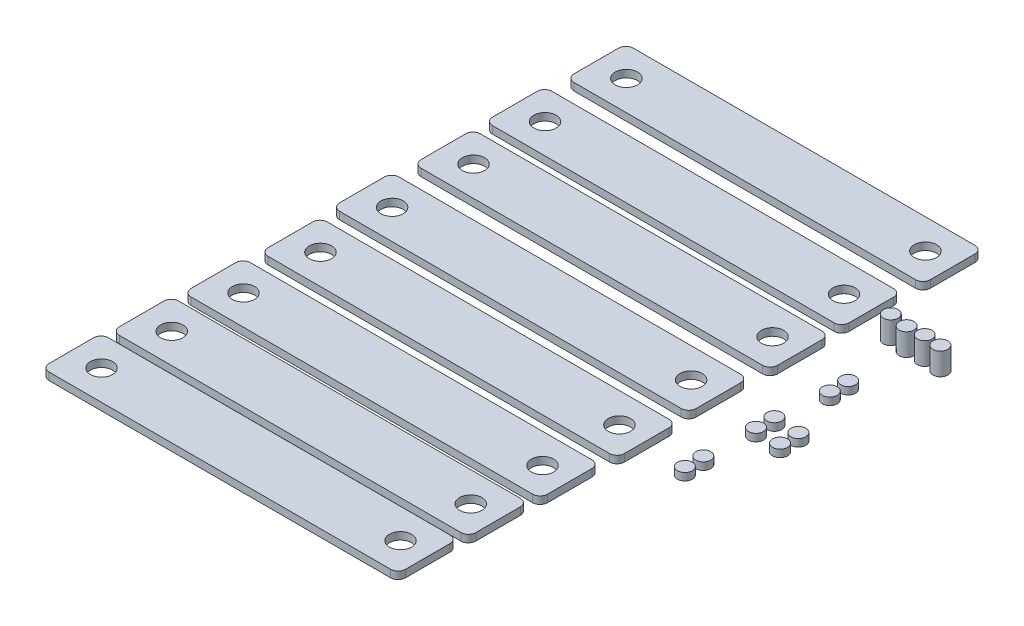
SolidWorks part; units mm, degrees
ref_plane "Front Plane" through (0, 0, 0) normal (0, 0, 1) x (1, 0, 0)
ref_plane "Top Plane" through (0, 0, 0) normal (0, 1, 0) x (1, 0, 0)
ref_plane "Right Plane" through (0, 0, 0) normal (1, 0, 0) x (0, 0, -1)
sketch "Sketch3" plane through (0, 0, 0) normal (0, 1, 0) x (1, 0, 0)
  line L0 (-120.2705, -22.8298) -> (109.7295, -22.8298)
  line L1 (-118.0489, 29.7498) -> (111.9511, 29.7498)
  line L2 (-123.0489, 24.7498) -> (-123.0489, -5.2502)
  line L3 (-118.0489, -10.2502) -> (111.9511, -10.2502)
  line L4 (116.9511, 24.7498) -> (116.9511, -5.2502)
  line L5 (-125.2705, -27.8298) -> (-125.2705, -57.8298)
  line L6 (-120.2705, -62.8298) -> (109.7295, -62.8298)
  line L7 (114.7295, -27.8298) -> (114.7295, -57.8298)
  line L8 (-120.3658, -122.7974) -> (109.6342, -122.7974)
  line L9 (-125.3658, -127.7974) -> (-125.3658, -157.7974)
  line L10 (-120.3658, -162.7974) -> (109.6342, -162.7974)
  line L11 (114.6342, -127.7974) -> (114.6342, -157.7974)
  line L12 (-118.1707, -73.1877) -> (111.8293, -73.1877)
  line L13 (-123.1707, -78.1877) -> (-123.1707, -108.1877)
  line L14 (-118.1707, -113.1877) -> (111.8293, -113.1877)
  line L15 (116.8293, -78.1877) -> (116.8293, -108.1877)
  line L16 (-122.1219, -169.334) -> (107.8781, -169.334)
  line L17 (-127.1219, -174.334) -> (-127.1219, -204.334)
  line L18 (-122.1219, -209.334) -> (107.8781, -209.334)
  line L19 (112.8781, -174.334) -> (112.8781, -204.334)
  line L20 (-118.7564, 78.6191) -> (111.2436, 78.6191)
  line L21 (-116.5347, 131.1987) -> (113.4653, 131.1987)
  line L22 (-121.5347, 126.1987) -> (-121.5347, 96.1987)
  line L23 (-116.5347, 91.1987) -> (113.4653, 91.1987)
  line L24 (118.4653, 126.1987) -> (118.4653, 96.1987)
  line L25 (-123.7564, 73.6191) -> (-123.7564, 43.6191)
  line L26 (-118.7564, 38.6191) -> (111.2436, 38.6191)
  line L27 (116.2436, 73.6191) -> (116.2436, 43.6191)
  line L28 (-124.3751, -214.3962) -> (105.6249, -214.3962)
  line L29 (-129.3751, -219.3962) -> (-129.3751, -249.3962)
  line L30 (-124.3751, -254.3962) -> (105.6249, -254.3962)
  line L31 (110.6249, -219.3962) -> (110.6249, -249.3962)
  circle A0 centre (-102.7337, 9.7498) radius 7.5
  circle A1 centre (98.5896, 9.7498) radius 7.5
  arc A2 (-123.0489, -5.2502) -> (-118.0489, -10.2502) centre (-118.0489, -5.2502) ccw
  arc A3 (-118.0489, 29.7498) -> (-123.0489, 24.7498) centre (-118.0489, 24.7498) ccw
  arc A4 (111.9511, 29.7498) -> (116.9511, 24.7498) centre (111.9511, 24.7498) cw
  arc A5 (111.9511, -10.2502) -> (116.9511, -5.2502) centre (111.9511, -5.2502) ccw
  circle A6 centre (-104.9554, -42.8298) radius 7.5
  circle A7 centre (96.3679, -42.8298) radius 7.5
  arc A8 (-125.2705, -57.8298) -> (-120.2705, -62.8298) centre (-120.2705, -57.8298) ccw
  arc A9 (-120.2705, -22.8298) -> (-125.2705, -27.8298) centre (-120.2705, -27.8298) ccw
  arc A10 (109.7295, -22.8298) -> (114.7295, -27.8298) centre (109.7295, -27.8298) cw
  arc A11 (109.7295, -62.8298) -> (114.7295, -57.8298) centre (109.7295, -57.8298) ccw
  circle A12 centre (-105.0507, -142.7974) radius 7.5
  circle A13 centre (96.2726, -142.7974) radius 7.5
  arc A14 (-125.3658, -157.7974) -> (-120.3658, -162.7974) centre (-120.3658, -157.7974) ccw
  arc A15 (-120.3658, -122.7974) -> (-125.3658, -127.7974) centre (-120.3658, -127.7974) ccw
  arc A16 (109.6342, -122.7974) -> (114.6342, -127.7974) centre (109.6342, -127.7974) cw
  arc A17 (109.6342, -162.7974) -> (114.6342, -157.7974) centre (109.6342, -157.7974) ccw
  circle A18 centre (-102.8556, -93.1877) radius 7.5
  circle A19 centre (98.4677, -93.1877) radius 7.5
  arc A20 (-123.1707, -108.1877) -> (-118.1707, -113.1877) centre (-118.1707, -108.1877) ccw
  arc A21 (-118.1707, -73.1877) -> (-123.1707, -78.1877) centre (-118.1707, -78.1877) ccw
  arc A22 (111.8293, -73.1877) -> (116.8293, -78.1877) centre (111.8293, -78.1877) cw
  arc A23 (111.8293, -113.1877) -> (116.8293, -108.1877) centre (111.8293, -108.1877) ccw
  circle A24 centre (-106.8068, -189.334) radius 7.5
  circle A25 centre (94.5165, -189.334) radius 7.5
  arc A26 (-127.1219, -204.334) -> (-122.1219, -209.334) centre (-122.1219, -204.334) ccw
  arc A27 (-122.1219, -169.334) -> (-127.1219, -174.334) centre (-122.1219, -174.334) ccw
  arc A28 (107.8781, -169.334) -> (112.8781, -174.334) centre (107.8781, -174.334) cw
  arc A29 (107.8781, -209.334) -> (112.8781, -204.334) centre (107.8781, -204.334) ccw
  circle A30 centre (149.537, 9.7498) radius 5
  circle A31 centre (149.537, -2.6047) radius 5
  circle A32 centre (145.8566, -36.2556) radius 5
  circle A33 centre (145.8566, -48.6101) radius 5
  circle A34 centre (144.7525, -82.9972) radius 5
  circle A35 centre (144.7525, -95.3516) radius 5
  circle A36 centre (163.1546, -37.3598) radius 5
  circle A37 centre (163.1546, -49.7142) radius 5
  circle A38 centre (-101.2195, 111.1987) radius 7.5
  circle A39 centre (100.1037, 111.1987) radius 7.5
  arc A40 (-121.5347, 96.1987) -> (-116.5347, 91.1987) centre (-116.5347, 96.1987) ccw
  arc A41 (-116.5347, 131.1987) -> (-121.5347, 126.1987) centre (-116.5347, 126.1987) ccw
  arc A42 (113.4653, 131.1987) -> (118.4653, 126.1987) centre (113.4653, 126.1987) cw
  arc A43 (113.4653, 91.1987) -> (118.4653, 96.1987) centre (113.4653, 96.1987) ccw
  circle A44 centre (-103.4412, 58.6191) radius 7.5
  circle A45 centre (97.8821, 58.6191) radius 7.5
  arc A46 (-123.7564, 43.6191) -> (-118.7564, 38.6191) centre (-118.7564, 43.6191) ccw
  arc A47 (-118.7564, 78.6191) -> (-123.7564, 73.6191) centre (-118.7564, 73.6191) ccw
  arc A48 (111.2436, 78.6191) -> (116.2436, 73.6191) centre (111.2436, 73.6191) cw
  arc A49 (111.2436, 38.6191) -> (116.2436, 43.6191) centre (111.2436, 43.6191) ccw
  circle A50 centre (-109.0599, -234.3962) radius 7.5
  circle A51 centre (92.2634, -234.3962) radius 7.5
  arc A52 (-129.3751, -249.3962) -> (-124.3751, -254.3962) centre (-124.3751, -249.3962) ccw
  arc A53 (-124.3751, -214.3962) -> (-129.3751, -219.3962) centre (-124.3751, -219.3962) ccw
  arc A54 (105.6249, -214.3962) -> (110.6249, -219.3962) centre (105.6249, -219.3962) cw
  arc A55 (105.6249, -254.3962) -> (110.6249, -249.3962) centre (105.6249, -249.3962) ccw
  point P0 (-3.0489, 9.7498)
  point P17 (-5.2705, -42.8298)
  point P34 (-5.3658, -142.7974)
  point P51 (-3.1707, -93.1877)
  point P68 (-7.1219, -189.334)
  point P101 (-1.5347, 111.1987)
  point P118 (-3.7564, 58.6191)
  point P135 (-9.3751, -234.3962)
  dimension "D1" = 15
  dimension "D3" = 5
  dimension "D4" = 5
  dimension "D7" = 15
  dimension "D9" = 5
  dimension "D10" = 5
  dimension "D13" = 15
  dimension "D15" = 5
  dimension "D16" = 5
  dimension "D19" = 15
  dimension "D21" = 5
  dimension "D22" = 5
  dimension "D25" = 15
  dimension "D27" = 5
  dimension "D28" = 5
  dimension "D31" = 10
  dimension "D32" = 15
  dimension "D34" = 5
  dimension "D35" = 5
  dimension "D38" = 15
  dimension "D40" = 5
extrude "Boss-Extrude2" add sketch "Sketch3" along normal blind 5
sketch "Sketch9" plane through (0, 5, 0) normal (0, 1, 0) x (1, 0, 0)
  circle A0 centre (140.0455, 47.9304) radius 5
  circle A1 centre (152.3486, 46.3163) radius 5
  circle A2 centre (163.6465, 47.2177) radius 5
  circle A3 centre (174.9862, 46.4234) radius 5
  point P2 (0, 0)
  dimension "D1" = 10
extrude "Boss-Extrude3" add sketch "Sketch9" along normal blind 15 separate body
